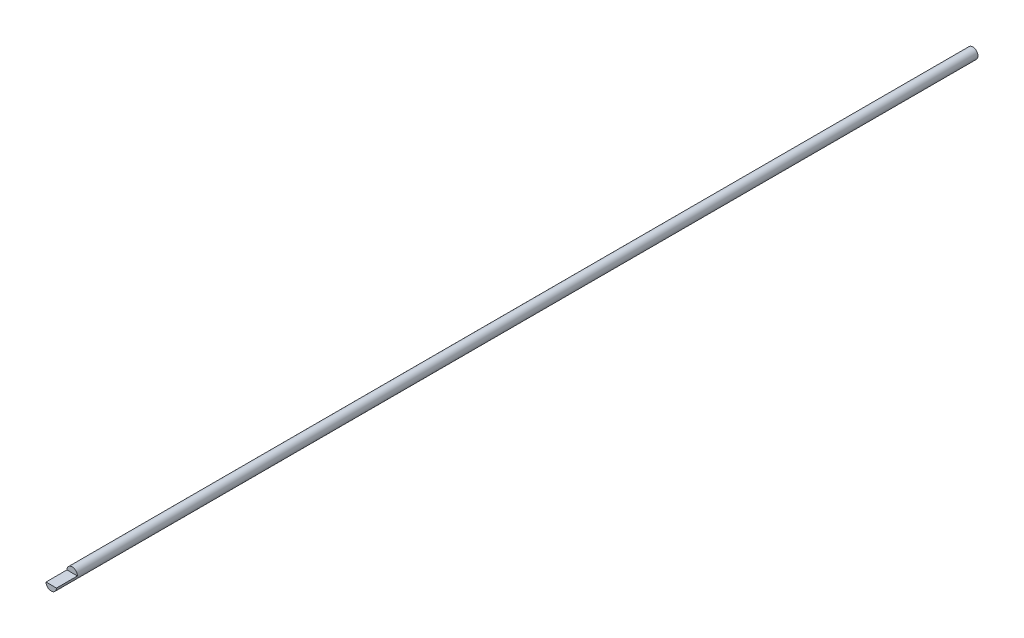
SolidWorks part; units mm, degrees
ref_plane "Front Plane" through (0, 0, 0) normal (0, 0, 1) x (1, 0, 0)
ref_plane "Top Plane" through (0, 0, 0) normal (0, 1, 0) x (1, 0, 0)
ref_plane "Right Plane" through (0, 0, 0) normal (1, 0, 0) x (0, 0, -1)
sketch "Sketch1" plane through (0, 0, 0) normal (0, 0, 1) x (1, 0, 0)
  circle A0 centre (0, 0) radius 3.175
  dimension "D1" = 6.35
extrude "Boss-Extrude1" add sketch "Sketch1" along normal blind 558.8
sketch "Sketch3" plane through (0, 0, 558.8) normal (0, 0, 1) x (1, 0, 0)
  line L0 (-3.175, 0) -> (3.175, 0)
  circle A1 centre (0, 0) radius 3.175
  arc A2 (3.175, 0) -> (-3.175, 0) centre (0, 0) ccw
  dimension "D1" = 0
extrude "Cut-Extrude1" cut sketch "Sketch3" against normal blind 12.7
